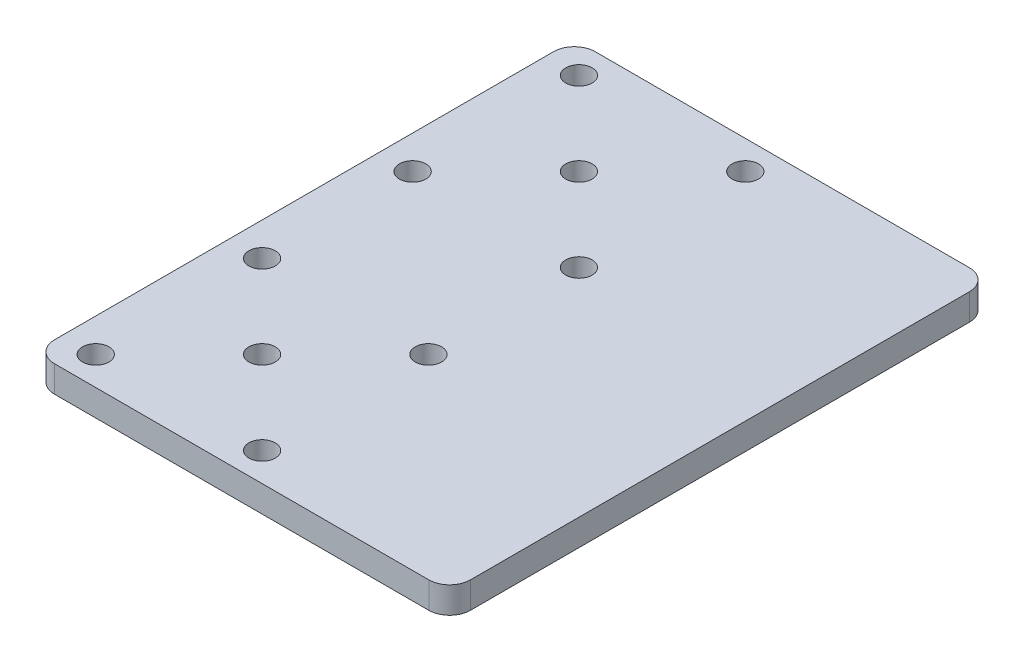
SolidWorks part; units mm, degrees
ref_plane "Front Plane" through (0, 0, 0) normal (0, 0, 1) x (1, 0, 0)
ref_plane "Top Plane" through (0, 0, 0) normal (0, 1, 0) x (1, 0, 0)
ref_plane "Right Plane" through (0, 0, 0) normal (1, 0, 0) x (0, 0, -1)
sketch "Sketch1" plane through (0, 0, 0) normal (0, 1, 0) x (1, 0, 0)
  line L0 (-50, -65) -> (-50, 65)
  line L1 (-50, -65) -> (50, -65)
  line L2 (-50, 65) -> (50, 65)
  line L3 (50, -65) -> (50, 65)
  line L4 (-50, -65) -> (50, 65) construction
  line L5 (-50, 65) -> (50, -65) construction
  point P1 (0, 0)
  dimension "D1" = 130
  dimension "D2" = 100
extrude "Boss-Extrude1" add sketch "Sketch1" along normal blind 6.35
fillet "Fillet1" radius 5 4 edges at (50, 3.175, -65) (-50, 3.175, -65) (-50, 3.175, 65) (50, 3.175, 65)
sketch "Sketch2" plane through (0, 6.35, 0) normal (0, 1, 0) x (1, 0, 0)
  line L0 (-42, -58.1) -> (-42, -18.1) construction
  line L1 (-42, -58.1) -> (-2, -58.1) construction
  line L2 (-42, -18.1) -> (-2, -18.1) construction
  line L3 (-2, -58.1) -> (-2, -18.1) construction
  line L4 (-42, -58.1) -> (-2, -18.1) construction
  line L5 (-42, -18.1) -> (-2, -58.1) construction
  line L6 (-50, 60) -> (-50, -60) construction
  point P1 (-22, -38.1)
  dimension "D1" = 40
  dimension "D2" = 40
  dimension "D3" = 8
  dimension "D4" = 18.1
hole_wizard "1/4 (0.25) Diameter Hole1" positions "Sketch4" profile "Sketch3" hole size "1/4" standard "ANSI Inch" end condition through all
sketch "Sketch4" plane through (0, 6.35, 0) normal (0, 1, 0) x (1, 0, 0)
  point P0 (-42, -18.1)
  point P3 (-2, -18.1)
  point P6 (-2, -58.1)
  point P9 (-42, -58.1)
  point P13 (-22, -38.1)
sketch "Sketch3" plane through (-42, 6.35, 18.1) normal (1, 0, 0) x (0, 0, 1)
  line L0 (0, 0) -> (0, 6.35)
  line L1 (0, 6.35) -> (3.175, 6.35)
  line L2 (3.175, 6.35) -> (3.175, 0)
  line L5 (3.175, 0) -> (0, 0)
  line L11 (0, -6.35) -> (0, 107.95) construction
  dimension "Thru Hole Dia." = 6.35
  dimension "Thru Hole Depth" = 6.35
mirror "Mirror1" about plane through (0, 0, 0) normal (0, 0, 1) of "1/4 (0.25) Diameter Hole1"
